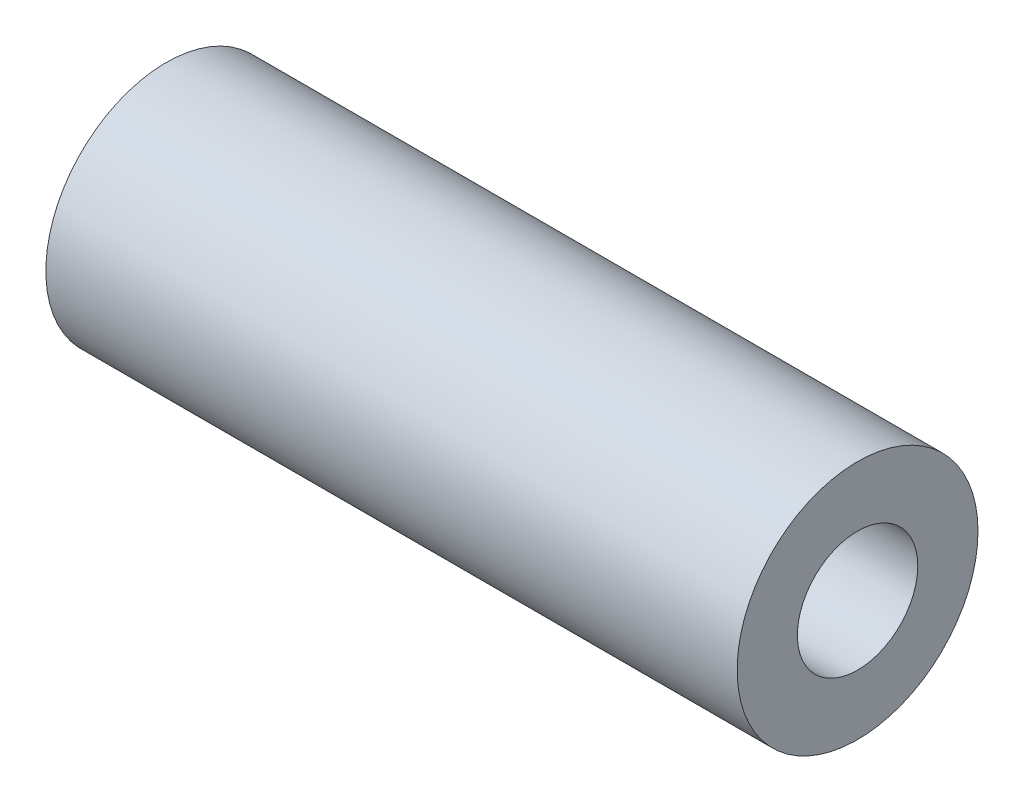
SolidWorks part; units mm, degrees
material "Delrin 2700 NC010, Low Viscosity Acetal Copolymer (SS)"
ref_plane "Front Plane" through (0, 0, 0) normal (0, 0, 1) x (1, 0, 0)
ref_plane "Top Plane" through (0, 0, 0) normal (0, 1, 0) x (1, 0, 0)
ref_plane "Right Plane" through (0, 0, 0) normal (1, 0, 0) x (0, 0, -1)
sketch "Sketch1" plane through (0, 0, 0) normal (1, 0, 0) x (0, 0, -1)
  circle A0 centre (0, 0) radius 6.35
  circle A1 centre (0, 0) radius 3.175
  dimension "D1" = 12.7
  dimension "D2" = 6.35
extrude "Boss-Extrude1" add sketch "Sketch1" along normal blind 36.449
